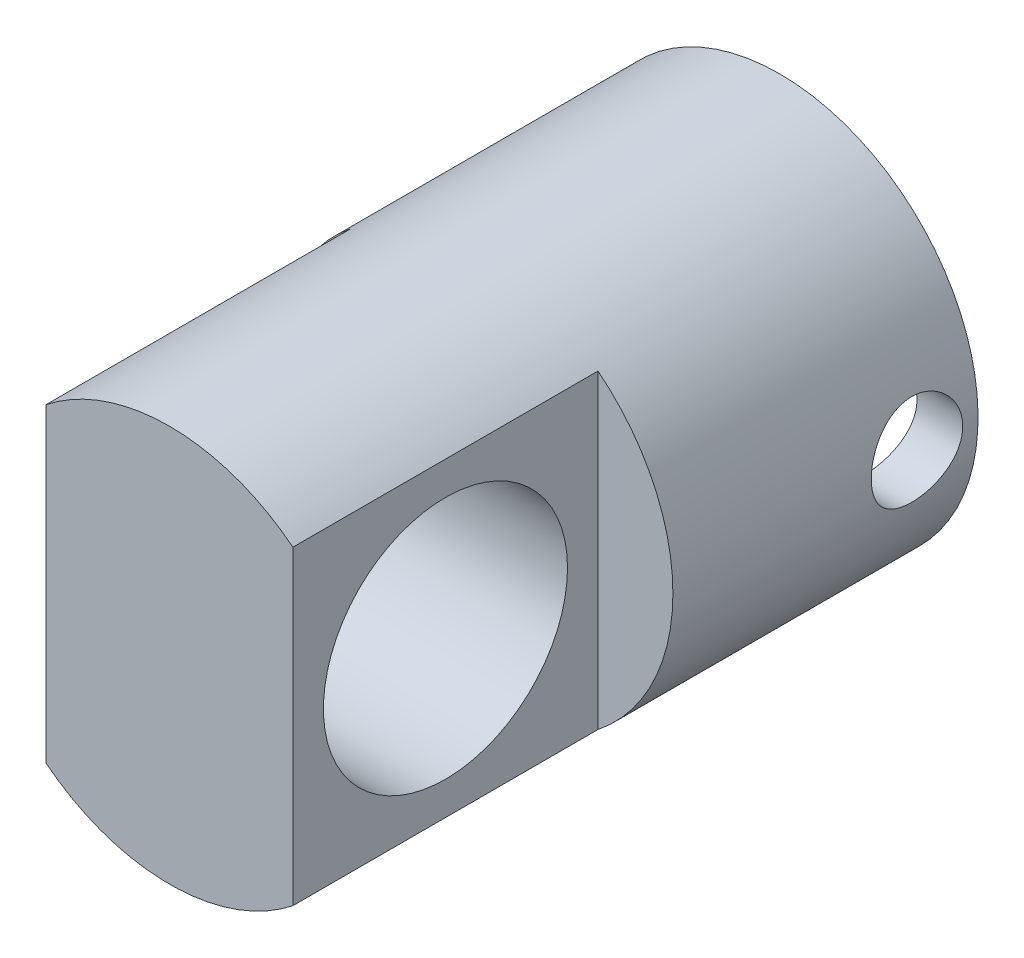
SolidWorks part; units mm, degrees
ref_plane "Front Plane" through (0, 0, 0) normal (0, 0, 1) x (1, 0, 0)
ref_plane "Top Plane" through (0, 0, 0) normal (0, 1, 0) x (1, 0, 0)
ref_plane "Right Plane" through (0, 0, 0) normal (1, 0, 0) x (0, 0, -1)
sketch "Sketch2" plane through (0, 0, 0) normal (1, 0, 0) x (0, 0, -1)
  line L2 (0, 0) -> (40, 0)
  line L3 (40, 0) -> (40, 3)
  line L4 (40, 3) -> (25, 3)
  line L5 (25, 3) -> (25, 13)
  line L6 (25, 13) -> (0, 13)
  line L7 (0, 13) -> (0, 0)
  dimension "D1" = 10
  dimension "D2" = 25
  dimension "D5" = 15
  dimension "D6" = 3
revolve "Revolve1" add sketch "Sketch2" angle 360 about L6
sketch "Sketch5" plane through (0, 0, 0) normal (0, 0, 1) x (1, 0, 0)
  line L0 (-8.0915, 23.1748) -> (8.0915, 23.1748)
  line L1 (-8.0915, 23.1748) -> (-8.0915, 2.7735)
  line L2 (8.0915, 23.1748) -> (8.0915, 2.7735)
  line L3 (-8.0915, 2.7735) -> (8.0915, 2.7735)
  circle A0 centre (0, 13) radius 13 construction
  arc A1 (-8.0915, 23.1748) -> (-8.0262, 2.7735) centre (0, 13) ccw
  arc A2 (8.0262, 2.7735) -> (8.0915, 23.1748) centre (0, 13) ccw
  circle M1 centre (0, 13) radius 13
extrude "Cut-Extrude1" cut sketch "Sketch5" against normal blind 20 contours L2 M1 | L1 M1
sketch "Sketch6" plane through (8.0915, 0, 0) normal (1, 0, 0) x (0, 0, -1)
  line L0 (0, 23.1748) -> (0, 2.8252) construction
  circle A0 centre (10, 13) radius 8
  dimension "D2" = 16
  dimension "D1" = 10
extrude "Cut-Extrude2" cut sketch "Sketch6" against normal blind 30
sketch "Sketch7" plane through (0, 0, 0) normal (1, 0, 0) x (0, 0, -1)
  line L0 (25, 3) -> (25, 23) construction
  circle A0 centre (36, 13) radius 3
  dimension "D2" = 6
  dimension "D1" = 11
extrude "Cut-Extrude3" cut sketch "Sketch7" against normal blind 30 and the other way blind 30
